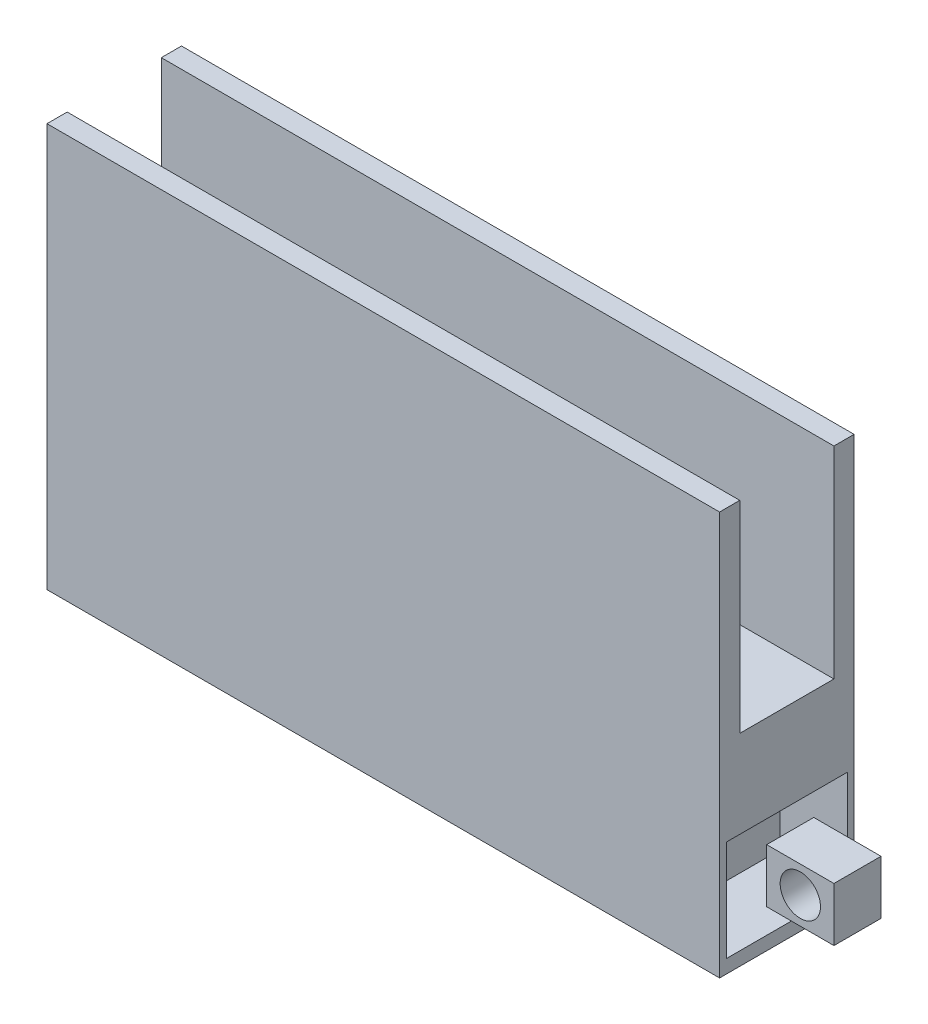
SolidWorks part; units mm, degrees
ref_plane "Front Plane" through (0, 0, 0) normal (0, 0, 1) x (1, 0, 0)
ref_plane "Top Plane" through (0, 0, 0) normal (0, 1, 0) x (1, 0, 0)
ref_plane "Right Plane" through (0, 0, 0) normal (1, 0, 0) x (0, 0, -1)
sketch "Sketch2" plane through (0, 0, 0) normal (0, 0, 1) x (1, 0, 0)
  line L0 (0, 0) -> (10, 0)
  line L1 (10, 0) -> (10, 2)
  line L2 (10, 2) -> (0, 2)
  line L3 (0, 2) -> (0, 0)
extrude "Boss-Extrude6" add sketch "Sketch2" along normal blind 2
sketch "Sketch7" plane through (10, 0, 0) normal (1, 0, 0) x (0, 0, -1)
  line L0 (0, 0) -> (0, 2) construction
  line L1 (-1.3, 1.3673) -> (-0.6, 1.3673)
  line L2 (-1.3, 1.3673) -> (-1.3, 0.5673)
  line L3 (-1.3, 0.5673) -> (-0.6, 0.5673)
  line L4 (-0.6, 1.3673) -> (-0.6, 0.5673)
  dimension "D1" = 0.7
  dimension "D2" = 0.8
  dimension "D3" = 0.6
extrude "Boss-Extrude9" add sketch "Sketch7" along normal blind 1
sketch "Sketch8" plane through (0, 0, 1.3) normal (0, 0, 1) x (1, 0, 0)
  line L0 (10.5, 0.9673) -> (10.5, 1.3673) construction
  line L2 (11, 0.9673) -> (10, 0.9673) construction
  line L3 (11, 1.3673) -> (11, 0.5673) construction
  line L4 (10, 1.3673) -> (10, 0.5673) construction
  line L5 (11, 1.3673) -> (10, 1.3673) construction
  circle A0 centre (10.5, 0.9673) radius 0.3
extrude "Cut-Extrude1" cut sketch "Sketch8" against normal blind 1
sketch "Sketch12" plane through (0, 2, 0) normal (0, 1, 0) x (1, 0, 0)
  line L1 (0, 0) -> (10, 0)
  line L2 (0, 0) -> (0, -2)
  line L3 (0, -2) -> (10, -2)
  line L4 (10, 0) -> (10, -2)
extrude "Boss-Extrude13" add sketch "Sketch12" along normal blind 4
sketch "Sketch13" plane through (10, 0, 0) normal (1, 0, 0) x (0, 0, -1)
  line L0 (-2, 0) -> (-2, 6) construction
  line L1 (-1.9, 1.7) -> (-0.1, 1.7)
  line L2 (-1.9, 1.7) -> (-1.9, 0.2)
  line L3 (-1.9, 0.2) -> (-0.1, 0.2)
  line L4 (-0.1, 1.7) -> (-0.1, 0.2)
  line L5 (-2, 0) -> (0, 0) construction
  dimension "D1" = 1.8
  dimension "D2" = 0.1
  dimension "D3" = 1.5
  dimension "D4" = 0.2
extrude "Cut-Extrude5" cut sketch "Sketch13" against normal blind 1
sketch "Sketch14" plane through (0, 6, 0) normal (0, 1, 0) x (1, 0, 0)
  line L0 (0, 0) -> (0, -2) construction
  line L1 (0, -0.3) -> (10, -0.3)
  line L2 (0, -0.3) -> (0, -1.7)
  line L3 (0, -1.7) -> (10, -1.7)
  line L4 (10, -0.3) -> (10, -1.7)
  line L5 (10, -2) -> (10, 0) construction
  line L7 (0, -2) -> (10, -2) construction
  dimension "D1" = 1.4
  dimension "D2" = 0.3
extrude "Cut-Extrude7" cut sketch "Sketch14" against normal blind 3
sketch "Sketch15" plane through (0, 0, 0) normal (-1, 0, 0) x (0, 0, 1)
  line L1 (0.3, 0.24) -> (1.7, 0.24)
  line L2 (0.3, 0.24) -> (0.3, 1.64)
  line L3 (0.3, 1.64) -> (1.7, 1.64)
  line L4 (1.7, 0.24) -> (1.7, 1.64)
  dimension "D1" = 1.4
extrude "Cut-Extrude9" cut sketch "Sketch15" against normal blind 4
sketch "Sketch16" plane through (0, 0, 0) normal (0, -1, 0) x (1, 0, 0)
  line L0 (0, 2) -> (0, 0) construction
  line L1 (0.24, 1.7) -> (3.24, 1.7)
  line L2 (0.24, 1.7) -> (0.24, 0.3)
  line L3 (0.24, 0.3) -> (3.24, 0.3)
  line L4 (3.24, 1.7) -> (3.24, 0.3)
  line L5 (0, 2) -> (10, 2) construction
  line L6 (0, 0) -> (10, 0) construction
  dimension "D1" = 0.24
  dimension "D2" = 0.3
  dimension "D3" = 0.3
  dimension "D4" = 3
extrude "Cut-Extrude10" cut sketch "Sketch16" against normal up to surface (1.64 mm away) up to face at (2, 1.64, 1)
